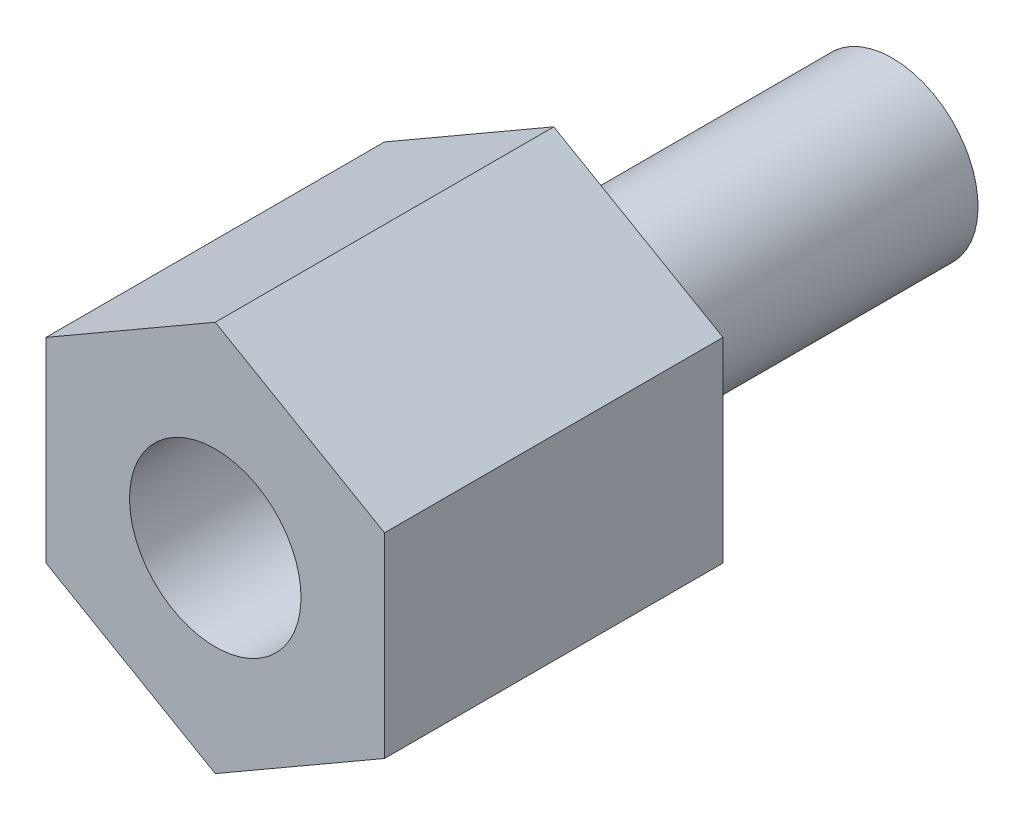
SolidWorks part; units mm, degrees
ref_plane "Front Plane" through (0, 0, 0) normal (0, 0, 1) x (1, 0, 0)
ref_plane "Top Plane" through (0, 0, 0) normal (0, 1, 0) x (1, 0, 0)
ref_plane "Right Plane" through (0, 0, 0) normal (1, 0, 0) x (0, 0, -1)
sketch "Sketch1" plane through (0, 0, 0) normal (0, 0, 1) x (1, 0, 0)
  line L1 (4.7625, 2.7496) -> (0, 5.4993)
  line L2 (0, 5.4993) -> (-4.7625, 2.7496)
  line L3 (-4.7625, 2.7496) -> (-4.7625, -2.7496)
  line L4 (-4.7625, -2.7496) -> (0, -5.4993)
  line L5 (0, -5.4993) -> (4.7625, -2.7496)
  line L6 (4.7625, -2.7496) -> (4.7625, 2.7496)
  circle A0 centre (0, 0) radius 4.7625 construction
  point P10 (0, -4.7625)
  dimension "Hex Size" = 9.525
sketch "Sketch2" plane through (0, 0, 0) normal (1, 0, 0) x (0, 0, -1)
  line L0 (9.525, 0) -> (-9.525, 0) construction
  line L2 (0, 2.413) -> (0, -2.413) construction
  line L3 (-4.7498, 2.413) -> (-4.7498, -2.413) construction
  line L4 (-10.2691, 2.4989) -> (-9.8723, 1.8115) construction
  line L5 (-9.8723, 1.8115) -> (-9.4754, 2.4989) construction
  line L6 (-9.4754, 2.4989) -> (-10.2691, 2.4989) construction
  line L7 (-10.2195, 2.413) -> (-9.525, 2.413) construction
  line L8 (-9.9219, 1.8974) -> (-9.8227, 1.8974) construction
  line L9 (-9.8723, 1.8974) -> (-9.8723, 1.8115) construction
  line L10 (-9.8723, 2.413) -> (-9.8723, 2.4989) construction
  line L11 (9.4754, 2.4989) -> (10.2691, 2.4989) construction
  line L12 (10.2691, 2.4989) -> (9.8723, 1.8115) construction
  line L13 (9.8723, 1.8115) -> (9.4754, 2.4989) construction
  line L14 (9.525, 2.413) -> (10.2195, 2.413) construction
  line L15 (9.8227, 1.8974) -> (9.9219, 1.8974) construction
  line L16 (9.8723, 1.8974) -> (9.8723, 1.8115) construction
  line L17 (9.8723, 2.413) -> (9.8723, 2.4989) construction
  line L18 (0, 5.4993) -> (-9.525, 5.4993) construction
  point P6 (0, 0)
  point P9 (-4.7498, 0)
  dimension "Thread Length (A)" = 9.525
  dimension "Screw Size Decimal Equivalent (A)" = 4.826
  dimension "Minimum Thread Length (B)" = 4.7752
  dimension "Thread Size (B)" = 4.826
  dimension "Thread Pitch (B)" = 0.7937
  dimension "Thread Pitch (B)/8" = 0.0992
  dimension "Thread Pitch (A)" = 0.7937
  dimension "Thread Pitch (A)/8" = 0.0992
  dimension "Length" = 9.525
sketch "Sketch3" plane through (0, 0, 0) normal (1, 0, 0) x (0, 0, -1)
  line L0 (-4.7498, 0) -> (9.525, 0)
  line L1 (-4.7498, 2.413) -> (-4.7498, -2.413) construction
  line L2 (9.525, 0) -> (9.525, 2.413)
  line L4 (9.525, 2.413) -> (1.4407, 2.413)
  line L5 (1.4407, 2.413) -> (1.143, 1.8974)
  line L6 (-4.7498, 0) -> (-4.7498, 2.413)
  line L8 (-4.7498, 2.413) -> (-9.525, 2.413)
  line L10 (9.525, 0) -> (9.525, -2.413) construction
  line L11 (-9.525, 2.413) -> (-9.525, 4.7625)
  line L12 (-9.525, 4.7625) -> (0, 4.7625)
  line L14 (1.143, 1.8974) -> (0, 1.8974)
  line L15 (0, 1.8974) -> (0, 4.7625)
  point P5 (-9.525, -4.7625)
  point P7 (0, 0)
  point P8 (-7.5406, -2.413)
  point P9 (7.5406, -2.413)
  point P10 (0, 0)
  point P18 (0, 0)
  point P22 (0, 0)
  point P23 (0, 0)
  point P27 (0, 1.8974)
  dimension "D6" = 1.9844
  dimension "D7" = 60
  dimension "D3" = 1.9844
  dimension "D5" = 1.143
revolve "Revolve1" add sketch "Sketch3" angle 360 about L0
sketch "Sketch4" plane through (0, 0, 9.525) normal (0, 0, 1) x (1, 0, 0)
  line L0 (0, 4.7625) -> (0, 2.413) construction
  line L1 (-4.7625, 2.7496) -> (-4.7625, -2.7496)
  line L2 (-4.7625, -2.7496) -> (0, -5.4993)
  line L3 (0, -5.4993) -> (4.7625, -2.7496)
  line L4 (4.7625, -2.7496) -> (4.7625, 2.7496)
  line L5 (4.7625, 2.7496) -> (0, 5.4993)
  line L6 (0, 5.4993) -> (-4.7625, 2.7496)
  circle A0 centre (0, 0) radius 4.7625 construction
  circle A1 centre (0, 0) radius 3.5877
  circle A2 centre (0, 0) radius 4.7625 construction
  point P16 (0, 3.5877)
extrude "Boss-Extrude1" add sketch "Sketch4" against normal up to surface (9.525 mm away) up to face at (0, 4.7625, 0)
equation "\"Thread Pitch (B)/8@Sketch2\" = \"Thread Pitch (B)@Sketch2\" / 8"
equation "\"Thread Pitch (A)/8@Sketch2\" = \"Thread Pitch (A)@Sketch2\" / 8"
equation "\"D6@Sketch3\" = \"Thread Pitch (A)@Sketch2\" * 2.5"
equation "\"D3@Sketch3\" = \"Thread Pitch (B)@Sketch2\" * 2.5"
equation "\"D5@Sketch3\" = \"Thread Length (A)@Sketch2\" * .12"
